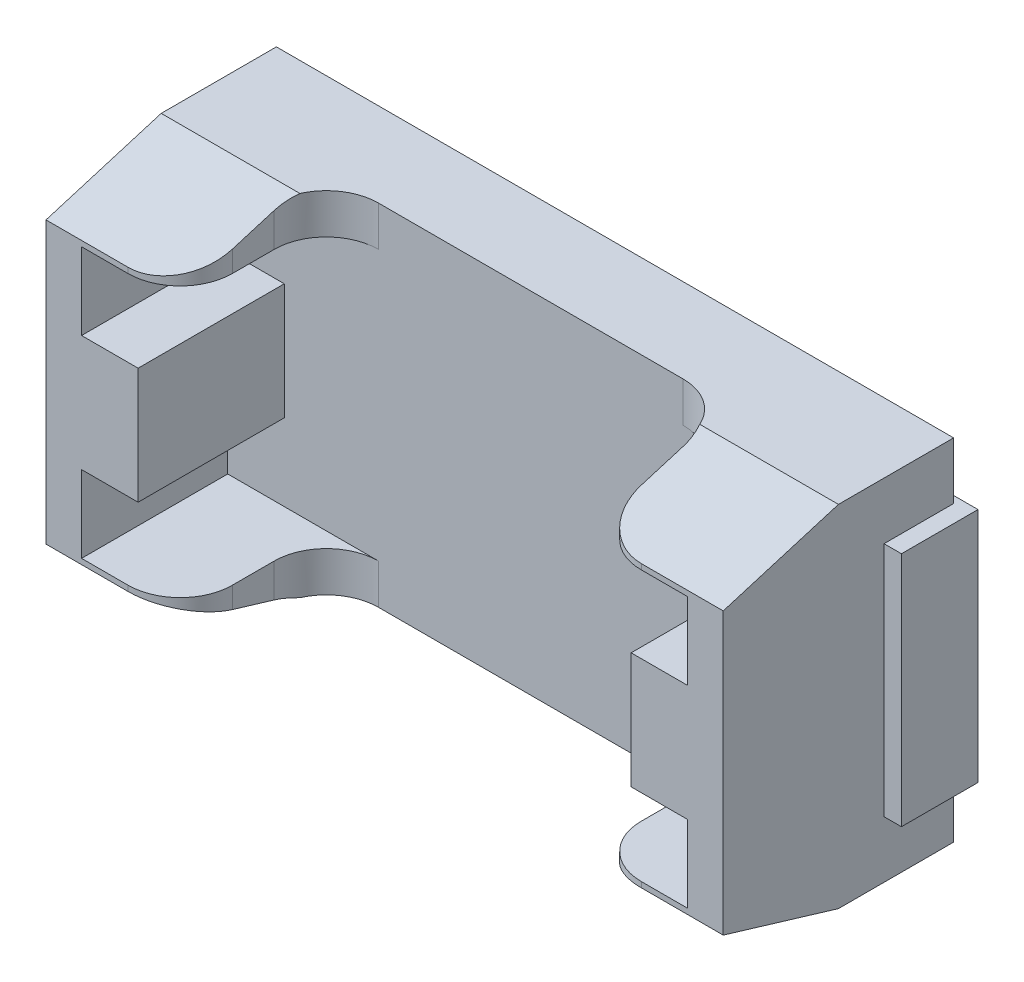
SolidWorks part; units mm, degrees
material "Plastique personnalisé"
ref_plane "Plan de face" through (0, 0, 0) normal (0, 0, 1) x (1, 0, 0)
ref_plane "Plan de dessus" through (0, 0, 0) normal (0, 1, 0) x (1, 0, 0)
ref_plane "Plan de droite" through (0, 0, 0) normal (1, 0, 0) x (0, 0, -1)
sketch "Esquisse1" plane through (0, 0, 0) normal (0, 0, 1) x (1, 0, 0)
  line L1 (-4.865, -2.515) -> (4.865, -2.515)
  line L2 (-4.865, -2.515) -> (-4.865, 2.515)
  line L3 (-4.865, 2.515) -> (4.865, 2.515)
  line L4 (4.865, -2.515) -> (4.865, 2.515)
  line L5 (-4.865, -2.515) -> (4.865, 2.515) construction
  line L6 (-4.865, 2.515) -> (4.865, -2.515) construction
  point P0 (0, 0)
  dimension "D1" = 9.73
  dimension "D2" = 5.03
extrude "Boss.-Extru.1" add sketch "Esquisse1" along normal blind 3.31
sketch "Esquisse2" plane through (0, 0, 0) normal (0, 0, -1) x (-1, 0, 0)
  line L0 (0, 0) -> (-5.31, 0) construction
  line L2 (0, 0) -> (0, -2.515) construction
  line L3 (4.865, -2.515) -> (-4.865, -2.515) construction
  dimension "D1" = 5.31
sketch "Esquisse3" plane through (0, 0, 0) normal (0, 0, -1) x (-1, 0, 0)
  line L0 (-5.31, 0) -> (-3.1944, 0) construction
  line L1 (0, 0) -> (-5.31, 0) construction
  line L2 (-3.1944, 1.6983) -> (-3.1944, -1.6983) construction
  line L3 (0, 0) -> (0, -2.515) construction
  line L4 (-1.2737, 1.6983) -> (-5.115, 1.6983)
  line L5 (-1.2737, 1.6983) -> (-1.2737, -1.6983)
  line L6 (-1.2737, -1.6983) -> (-5.115, -1.6983)
  line L7 (-5.115, 1.6983) -> (-5.115, -1.6983)
  line L8 (-1.2737, 1.6983) -> (-5.115, -1.6983) construction
  line L9 (-1.2737, -1.6983) -> (-5.115, 1.6983) construction
  line L10 (1.2737, 1.6983) -> (1.2737, -1.6983)
  line L11 (1.2737, 1.6983) -> (5.115, 1.6983)
  line L12 (5.115, 1.6983) -> (5.115, -1.6983)
  line L13 (1.2737, -1.6983) -> (5.115, -1.6983)
extrude "Boss.-Extru.2" add sketch "Esquisse3" along normal blind 0.1 and the other way blind 1
sketch "Esquisse4" plane through (4.865, 0, 0) normal (1, 0, 0) x (0, 0, -1)
  line L0 (-1.655, -2.515) -> (-3.31, -2.0172)
  line L1 (-3.31, -2.515) -> (0, -2.515) construction
  line L2 (-3.31, -2.515) -> (-3.31, 2.515) construction
  line L3 (-3.31, 0) -> (-2.1067, 0) construction
  line L4 (-1.655, 2.515) -> (-3.31, 2.0172)
  line L5 (-3.31, -2.0172) -> (-3.31, 2.0172)
  line L6 (-1.655, -2.515) -> (-1.655, -2.6887)
  line L7 (-1.655, -2.6887) -> (-3.4549, -2.6887)
  line L8 (-3.4549, -2.6887) -> (-3.4262, 2.639)
  line L9 (-3.4262, 2.639) -> (-1.655, 2.6024)
  line L10 (-1.655, 2.6024) -> (-1.655, 2.515)
extrude "Enlèv. mat.-Extru.1" cut sketch "Esquisse4" against normal through all
sketch "Esquisse5" plane through (0, 0, 3.31) normal (0, 0, 1) x (1, 0, 0)
  line L1 (2.937, -2.9154) -> (-2.937, -2.9154)
  line L2 (2.937, -2.9154) -> (2.937, 3.0135)
  line L3 (2.937, 3.0135) -> (-2.937, 3.0135)
  line L4 (-2.937, -2.9154) -> (-2.937, 3.0135)
  line L5 (2.937, -2.9154) -> (-2.937, 3.0135) construction
  line L6 (2.937, 3.0135) -> (-2.937, -2.9154) construction
  point P0 (0, 0.0491)
extrude "Enlèv. mat.-Extru.2" cut sketch "Esquisse5" against normal blind 2.1
sketch "Esquisse6" plane through (0, 0, 3.31) normal (0, 0, 1) x (1, 0, 0)
  line L0 (4.354, 0) -> (-4.354, 0) construction
  line L1 (-4.354, -1.9387) -> (4.354, -1.9387)
  line L2 (-4.354, -1.9387) -> (-4.354, -0.834)
  line L3 (-4.354, 1.9387) -> (4.354, 1.9387)
  line L4 (4.354, -1.9387) -> (4.354, -0.834)
  line L5 (-4.354, -1.9387) -> (4.354, 1.9387) construction
  line L6 (-4.354, 1.9387) -> (4.354, -1.9387) construction
  line L7 (-4.354, 0.834) -> (-4.354, 1.9387)
  line L8 (-4.354, -0.834) -> (-3.5416, -0.834)
  line L9 (-5.1663, -0.834) -> (-5.1663, 0.834)
  line L10 (-4.354, 0.834) -> (-3.5416, 0.834)
  line L11 (-3.5416, -0.834) -> (-3.5416, 0.834)
  line L12 (-4.354, 0) -> (-3.5416, 0.834) construction
  line L13 (-4.354, 0) -> (-3.5416, -0.834) construction
  line L14 (0, 0) -> (0, -2.515) construction
  line L15 (4.354, 0) -> (3.5416, -0.834) construction
  line L16 (4.354, 0) -> (3.5416, 0.834) construction
  line L17 (3.5416, -0.834) -> (3.5416, 0.834)
  line L18 (4.354, 0.834) -> (3.5416, 0.834)
  line L19 (4.354, -0.834) -> (3.5416, -0.834)
  line L20 (4.354, 0.834) -> (4.354, 1.9387)
  point P0 (0, 0)
  line M2 (-2.937, -2.0172) -> (-2.937, 2.0172)
extrude "Enlèv. mat.-Extru.4" cut sketch "Esquisse6" against normal blind 2.1 contours L18 L20 L3 L1 L4 L19 L17 M2 | L11 L8 L2 L1 L3 L7 L10 M2
fillet "Congé1" radius 0.75 4 edges at (-2.937, 2.2269, 1.21) (2.937, 2.2269, 1.21) (2.937, -2.2269, 1.21) (-2.937, -2.2269, 1.21)
fillet "Congé2" radius 0.75 4 edges at (2.937, -1.9779, 3.31) (2.937, 1.9779, 3.31) (-2.937, 1.9779, 3.31) (-2.937, -1.9779, 3.31)
